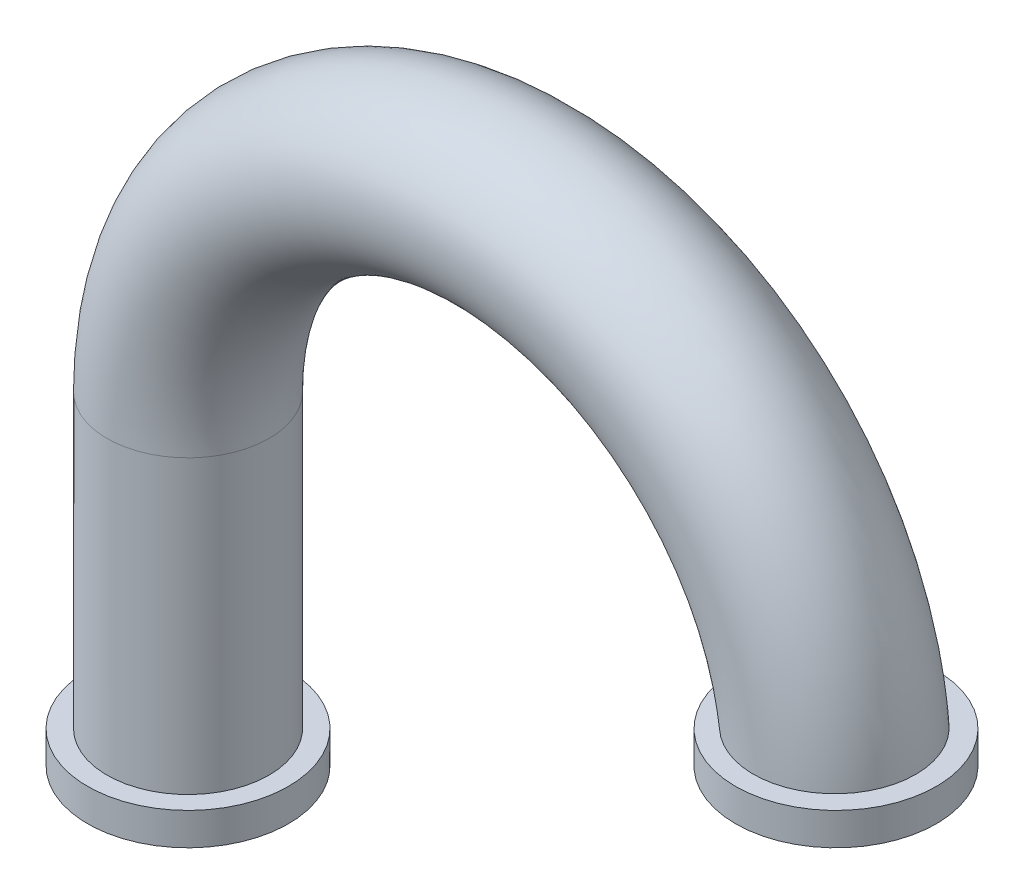
SolidWorks part; units mm, degrees
ref_plane "Front Plane" through (0, 0, 0) normal (0, 0, 1) x (1, 0, 0)
ref_plane "Top Plane" through (0, 0, 0) normal (0, 1, 0) x (1, 0, 0)
ref_plane "Right Plane" through (0, 0, 0) normal (1, 0, 0) x (0, 0, -1)
sketch "Sketch1" plane through (0, 0, 0) normal (0, 0, 1) x (1, 0, 0)
  line L0 (-2, 0) -> (-2, -1)
  arc A0 (0, 0) -> (-2, 0) centre (-1, 0) ccw
sketch "Sketch3" plane through (0, 0, 0) normal (0, 1, 0) x (1, 0, 0)
  circle A0 centre (0, 0) radius 0.2
sweep "Sweep-Thin1" add profiles "Sketch3" path "Sketch1" parameters "D1"=0.05
sketch "Sketch5" plane through (0, 0, 0) normal (0, 0, 1) x (1, 0, 0)
  line L0 (0, 0) -> (0, 0.1)
sketch "Sketch6" plane through (0, 0, 0) normal (0, 1, 0) x (1, 0, 0)
  circle A0 centre (0, 0) radius 0.21
sweep "Sweep-Thin2" add profiles "Sketch6" path "Sketch5" parameters "D1"=0.1
sketch "Sketch7" plane through (0, -1, 0) normal (0, -1, 0) x (-1, 0, 0)
  point P1 (2, 0)
ref_plane "Plane1" through (-2, 0, 0) normal (1, 0, 0) x (0, 0, -1)
sketch "Sketch9" plane through (-2, 0, 0) normal (1, 0, 0) x (0, 0, -1)
  line L0 (0, -1) -> (0, -0.9)
ref_plane "Plane2" through (0, -1, 0) normal (0, -1, 0) x (-1, 0, 0)
sketch "Sketch10" plane through (0, -1, 0) normal (0, -1, 0) x (-1, 0, 0)
  circle A0 centre (2, 0) radius 0.21
sweep "Sweep-Thin3" add profiles "Sketch10" path "Sketch9" parameters "D1"=0.1
